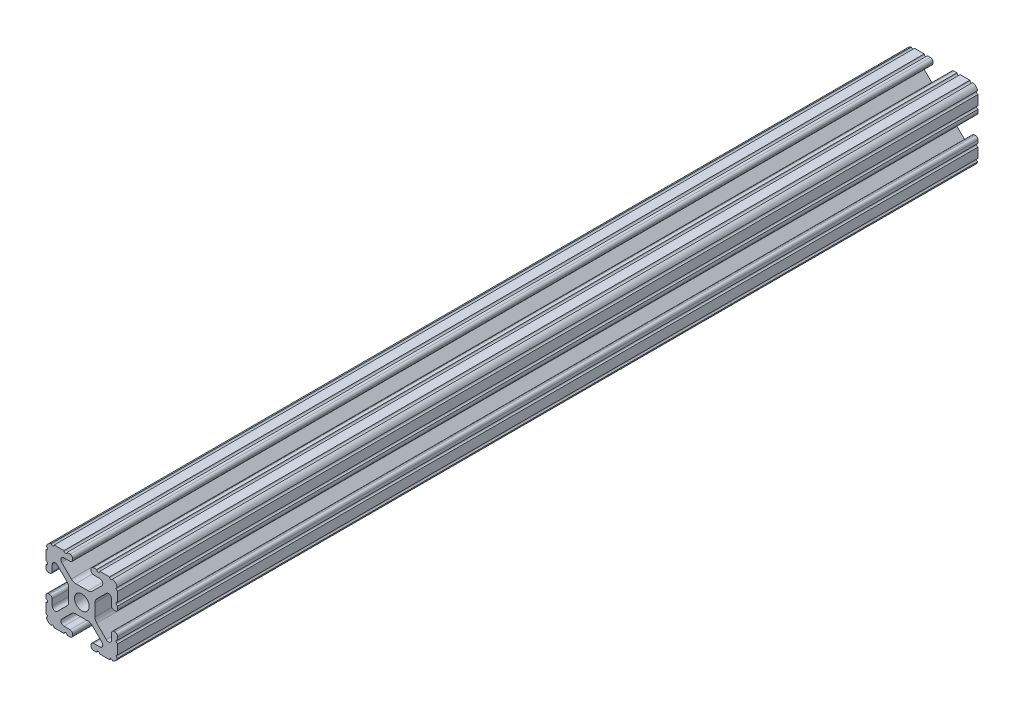
SolidWorks part; units mm, degrees
material "6061 Alloy"
ref_plane "Front Plane" through (0, 0, 0) normal (0, 0, 1) x (1, 0, 0)
ref_plane "Top Plane" through (0, 0, 0) normal (0, 1, 0) x (1, 0, 0)
ref_plane "Right Plane" through (0, 0, 0) normal (1, 0, 0) x (0, 0, -1)
sketch "Sketch2" plane through (0, 0, 0) normal (0, 0, 1) x (1, 0, 0)
  line L0 (0, 12.7) -> (0, -12.7) construction
  line L1 (-12.7, 0) -> (12.7, 0) construction
  line L2 (3.2512, -12.7) -> (12.7, -12.7)
  line L3 (12.7, -12.7) -> (12.7, -3.2512)
  line L4 (3.2512, -12.7) -> (3.2512, -10.4902)
  line L5 (3.2512, -10.4902) -> (8.9276, -10.4902)
  line L6 (8.9276, -10.4902) -> (3.0856, -4.6482)
  line L7 (0, 0) -> (12.7, -12.7) construction
  line L8 (12.7, -3.2512) -> (10.4902, -3.2512)
  line L9 (10.4902, -3.2512) -> (10.4902, -8.9276)
  line L10 (10.4902, -8.9276) -> (4.6482, -3.0856)
  circle A0 centre (0, 0) radius 2.6035
  arc A1 (6.3485, -10.4902) -> (7.1039, -8.6665) centre (6.3485, -9.4219) ccw construction
  point P8 (0, -4.6482)
  dimension "Center Hole Diameter" = 5.207
  dimension "Rail Height" = 25.4
  dimension "Rail Width" = 25.4
  dimension "T-Slot Width" = 6.5024
  dimension "Slot Inner Width" = 14.8336
  dimension "Thickness" = 2.2098
  dimension "Slot Depth" = 5.842
  dimension "D1" = 2.2098
sketch "Sketch3" plane through (0, 0, 0) normal (1, 0, 0) x (0, 0, -1)
  line L0 (-304.8, -12.7) -> (304.8, -12.7) construction
  line L1 (-279.4, 0) -> (279.4, 0) construction
  dimension "Length" = 609.6
  dimension "D1" = 25.4
sketch "Sketch4" plane through (0, 0, 0) normal (0, 0, 1) x (1, 0, 0)
  line L0 (4.1904, -12.7) -> (10.1173, -12.7)
  line L1 (3.2512, -12.7) -> (12.7, -12.7) construction
  line L2 (3.2512, -12.7) -> (3.2512, -10.4902) construction
  line L3 (3.2512, -10.4902) -> (8.9276, -10.4902) construction
  line L4 (3.2512, -11.4294) -> (3.2512, -11.7608)
  line L5 (4.1904, -10.4902) -> (6.3485, -10.4902)
  line L6 (0, -4.6482) -> (2.164, -4.6482)
  line L7 (8.9276, -10.4902) -> (3.0856, -4.6482) construction
  line L8 (3.7373, -5.2999) -> (7.1039, -8.6665)
  line L9 (12.7, -12.7) -> (12.7, -3.2512) construction
  line L10 (10.4902, -8.9276) -> (4.6482, -3.0856) construction
  line L11 (10.4902, -3.2512) -> (10.4902, -8.9276) construction
  line L12 (10.4902, -6.3485) -> (10.4902, -4.1904)
  line L13 (12.7, -3.2512) -> (10.4902, -3.2512) construction
  line L14 (11.4294, -3.2512) -> (11.7608, -3.2512)
  line L15 (12.7, -4.1904) -> (12.7, -10.1173)
  line L16 (8.6665, -7.1039) -> (5.2999, -3.7373)
  line L17 (4.6482, 0) -> (4.6482, -2.164)
  line L18 (-12.7, 0) -> (12.7, 0) construction
  line L19 (0, -4.6482) -> (0, -2.6035)
  line L20 (0, 12.7) -> (0, -12.7) construction
  line L21 (4.6482, 0) -> (2.6035, 0)
  arc A0 (3.2512, -11.7608) -> (4.1904, -12.7) centre (4.1904, -11.7608) ccw
  arc A2 (3.2512, -11.4294) -> (4.1904, -10.4902) centre (4.1904, -11.4294) cw
  arc A3 (6.3485, -10.4902) -> (7.1039, -8.6665) centre (6.3485, -9.4219) ccw
  arc A4 (2.164, -4.6482) -> (3.7373, -5.2999) centre (2.164, -6.8732) cw
  arc A5 (10.1173, -12.7) -> (12.7, -10.1173) centre (10.1173, -10.1173) ccw
  arc A6 (8.6665, -7.1039) -> (10.4902, -6.3485) centre (9.4219, -6.3485) ccw
  arc A7 (10.4902, -4.1904) -> (11.4294, -3.2512) centre (11.4294, -4.1904) cw
  arc A8 (11.7608, -3.2512) -> (12.7, -4.1904) centre (11.7608, -4.1904) cw
  arc A9 (5.2999, -3.7373) -> (4.6482, -2.164) centre (6.8732, -2.164) cw
  circle A10 centre (0, 0) radius 2.6035 construction
  arc A11 (0, -2.6035) -> (2.6035, 0) centre (0, 0) ccw
  dimension "D1" = 2.5827
  dimension "D2" = 2.225
  dimension "D3" = 0.9392
extrude "Boss-Extrude1" add sketch "Sketch4" along normal mid plane 609.6
sketch "Sketch5" plane through (0, 0, 0) normal (0, 0, 1) x (1, 0, 0)
  line L0 (3.2512, -12.7) -> (12.7, -12.7) construction
  line L1 (4.1904, -10.4902) -> (6.3485, -10.4902) construction
  line L3 (0, 0) -> (12.7, -12.7) construction
  line L4 (6.3485, -10.4902) -> (6.3485, -12.7) construction
  line L5 (8.9276, -10.4902) -> (3.0856, -4.6482) construction
  circle A0 centre (10.3562, -12.7) radius 0.5524
  circle A1 centre (5.796, -12.7) radius 0.5524
  circle A2 centre (12.7, -10.3562) radius 0.5524
  circle A3 centre (12.7, -5.796) radius 0.5524
  point P10 (5.2694, -10.4902)
  point P12 (9.4219, -6.3485)
  dimension "D1" = 1.1049
extrude "Cut-Extrude1" cut sketch "Sketch5" against normal through all both and the other way through all
mirror "Mirror1" about plane through (0, 0, 0) normal (1, 0, 0) of bodies 137 134
mirror "Mirror2" about plane through (0, 0, 0) normal (0, 1, 0) of bodies 135
sketch "Sketch6" plane through (0, 0, -304.8) normal (0, 0, -1) x (-1, 0, 0)
  line L1 (-37.9045, 25.7252) -> (35.4927, 25.7252)
  line L2 (-37.9045, 25.7252) -> (-37.9045, -23.1527)
  line L3 (-37.9045, -23.1527) -> (35.4927, -23.1527)
  line L4 (35.4927, 25.7252) -> (35.4927, -23.1527)
extrude "Cut-Extrude2" cut sketch "Sketch6" against normal blind 304.8
equation "\"D1@Boss-Extrude1\"=\"Length@Sketch3\""
equation "\"D1@Sketch2\"=\"Thickness@Sketch2\""
equation "\"D2@Sketch4\"=\"Slot Inner Width@Sketch2\"*0.15"
equation "\"D1@Sketch4\"=\"D3@Sketch4\"*2.75"
equation "\"D3@Sketch4\"=\"Thickness@Sketch2\"*0.425"
equation "\"D1@Sketch5\"=\"Thickness@Sketch2\"*0.5"
